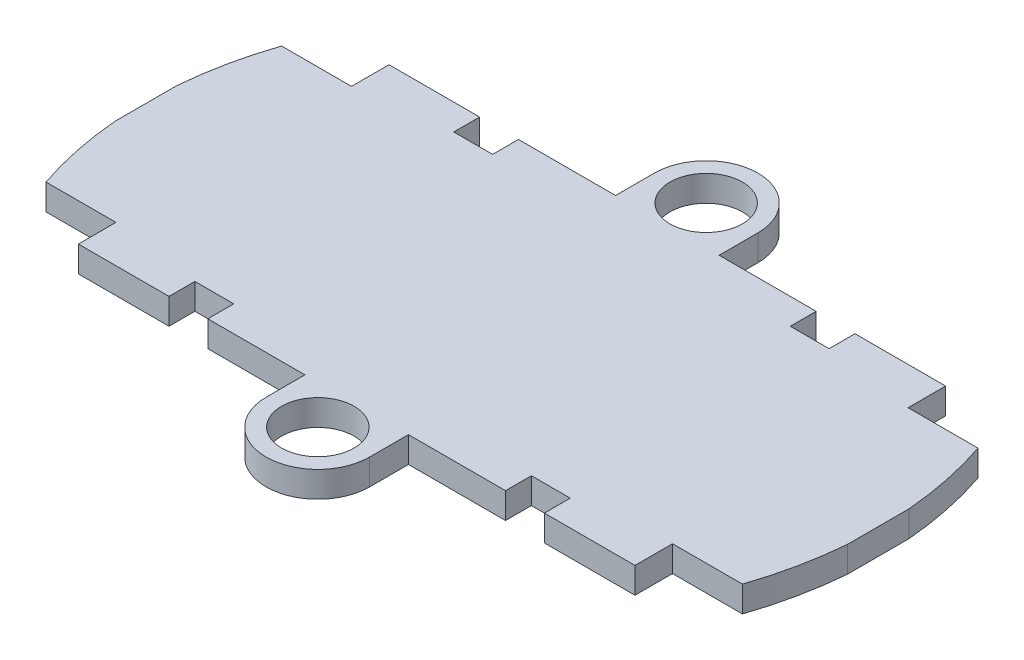
SolidWorks part; units mm, degrees
ref_plane "Front Plane" through (0, 0, 0) normal (0, 0, 1) x (1, 0, 0)
ref_plane "Top Plane" through (0, 0, 0) normal (0, 1, 0) x (1, 0, 0)
ref_plane "Right Plane" through (0, 0, 0) normal (1, 0, 0) x (0, 0, -1)
sketch "Sketch1" plane through (0, 0, 0) normal (0, 1, 0) x (1, 0, 0)
  line L1 (-35.941, -11.557) -> (35.941, -11.557)
  line L2 (-35.941, -11.557) -> (-35.941, 11.557)
  line L3 (-35.941, 11.557) -> (35.941, 11.557)
  line L4 (35.941, -11.557) -> (35.941, 11.557)
  line L5 (-35.941, -11.557) -> (35.941, 11.557) construction
  line L6 (-35.941, 11.557) -> (35.941, -11.557) construction
  line L7 (-27.305, -15.24) -> (27.305, -15.24)
  line L8 (-27.305, -15.24) -> (-27.305, 15.24)
  line L9 (-27.305, 15.24) -> (27.305, 15.24)
  line L10 (27.305, -15.24) -> (27.305, 15.24)
  line L11 (-27.305, -15.24) -> (27.305, 15.24) construction
  line L12 (-27.305, 15.24) -> (27.305, -15.24) construction
  point P0 (0, 0)
  point P6 (0, 0)
  dimension "D1" = 71.882
  dimension "D2" = 23.114
  dimension "D3" = 54.61
  dimension "D4" = 30.48
extrude "Boss-Extrude1" add sketch "Sketch1" along normal blind 2.54 contours L1 L10 L3 L8 | L1 L8 L3 L2 | L10 L1 L4 L3 | L7 L10 L1 L8 | L3 L10 L9 L8
sketch "Sketch2" plane through (0, 0, 0) normal (0, 1, 0) x (1, 0, 0)
  line L1 (-36.068, -36.068) -> (36.068, -36.068)
  line L2 (-36.068, -36.068) -> (-36.068, 36.068)
  line L3 (-36.068, 36.068) -> (36.068, 36.068)
  line L4 (36.068, -36.068) -> (36.068, 36.068)
  line L5 (-36.068, -36.068) -> (36.068, 36.068) construction
  line L6 (-36.068, 36.068) -> (36.068, -36.068) construction
  circle A0 centre (0, 0) radius 36.068
  dimension "D1" = 72.136
  dimension "D2" = 72.136
extrude "Cut-Extrude1" cut sketch "Sketch2" against normal through all both and the other way through all contours A0 L3 L2 | A0 L4 L3 | A0 L1 L4 | A0 L2 L1
sketch "Sketch3" plane through (0, 0, 0) normal (0, 1, 0) x (1, 0, 0)
  line L1 (-5.08, 19.05) -> (-5.08, 15.24)
  line L2 (-27.305, 15.24) -> (27.305, 15.24) construction
  line L3 (5.08, 19.05) -> (5.08, 15.24)
  line L4 (-5.08, 15.24) -> (5.08, 15.24)
  line L5 (-1.397, 0) -> (1.397, 0) construction
  line L7 (-5.08, -19.05) -> (-5.08, -15.24)
  line L8 (5.08, -19.05) -> (5.08, -15.24)
  line L9 (-5.08, -15.24) -> (5.08, -15.24)
  circle A0 centre (0, 19.05) radius 3.556
  circle A1 centre (0, -19.05) radius 3.556
  arc A2 (5.08, 19.05) -> (-5.08, 19.05) centre (0, 19.05) ccw
  arc A3 (5.08, -19.05) -> (-5.08, -19.05) centre (0, -19.05) cw
extrude "Boss-Extrude2" add sketch "Sketch3" along normal blind 2.54
sketch "Sketch4" plane through (0, 0, 0) normal (0, 1, 0) x (1, 0, 0)
  line L0 (-1.397, 0) -> (1.397, 0) construction
  line L1 (-18.415, -15.24) -> (-14.605, -15.24)
  line L2 (-18.415, -15.24) -> (-18.415, -12.7)
  line L3 (-18.415, -12.7) -> (-14.605, -12.7)
  line L4 (-14.605, -15.24) -> (-14.605, -12.7)
  line L5 (-18.415, 15.24) -> (-18.415, 12.7)
  line L6 (-18.415, 15.24) -> (-14.605, 15.24)
  line L7 (-14.605, 15.24) -> (-14.605, 12.7)
  line L8 (-18.415, 12.7) -> (-14.605, 12.7)
  line L9 (0, -1.397) -> (0, 1.397) construction
  line L10 (14.605, 15.24) -> (14.605, 12.7)
  line L11 (18.415, 15.24) -> (14.605, 15.24)
  line L12 (18.415, 15.24) -> (18.415, 12.7)
  line L13 (18.415, 12.7) -> (14.605, 12.7)
  line L14 (14.605, -15.24) -> (14.605, -12.7)
  line L15 (18.415, -12.7) -> (14.605, -12.7)
  line L16 (18.415, -15.24) -> (18.415, -12.7)
  line L17 (18.415, -15.24) -> (14.605, -15.24)
  dimension "D1" = 2.54
  dimension "D2" = 3.81
extrude "Cut-Extrude3" cut sketch "Sketch4" along normal through all contours L5 L8 L7 L6 | L13 L12 L11 L10 | L1 L4 L3 L2 | L17 L16 L15 L14
